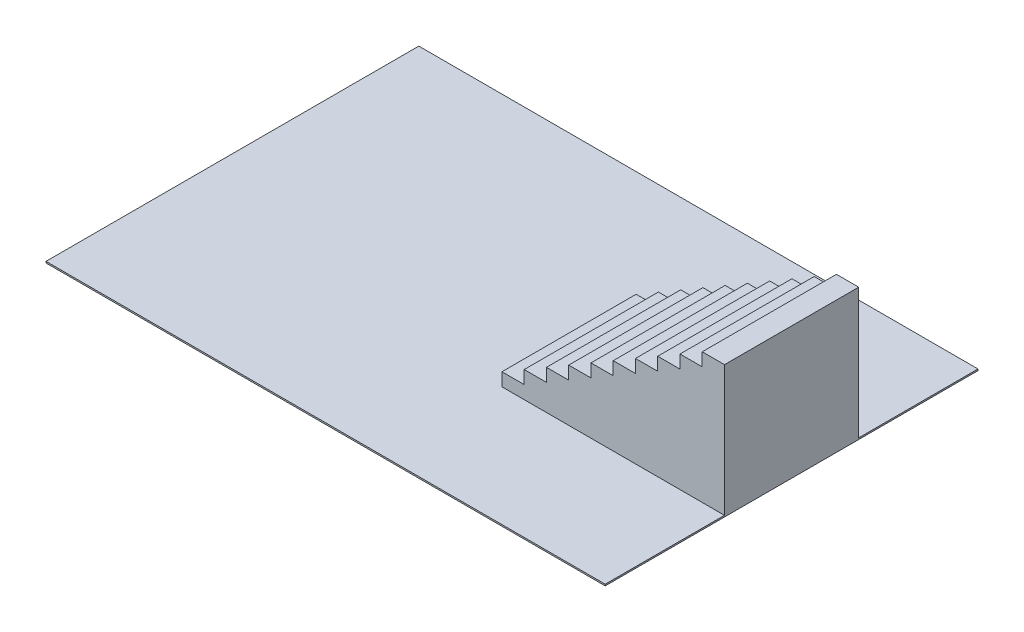
SolidWorks part; units mm, degrees
ref_plane "Front Plane" through (0, 0, 0) normal (0, 0, 1) x (1, 0, 0)
ref_plane "Top Plane" through (0, 0, 0) normal (0, 1, 0) x (1, 0, 0)
ref_plane "Right Plane" through (0, 0, 0) normal (1, 0, 0) x (0, 0, -1)
sketch "Sketch1" plane through (0, 0, 0) normal (0, 1, 0) x (1, 0, 0)
  line L1 (952.5, 635) -> (-952.5, 635)
  line L2 (952.5, 635) -> (952.5, -635)
  line L3 (952.5, -635) -> (-952.5, -635)
  line L4 (-952.5, 635) -> (-952.5, -635)
  line L5 (952.5, 635) -> (-952.5, -635) construction
  line L6 (952.5, -635) -> (-952.5, 635) construction
  point P0 (0, 0)
  dimension "D1" = 1270
  dimension "D2" = 1905
extrude "Boss-Extrude1" add sketch "Sketch1" along normal blind 5.08
sketch "Sketch2" plane through (0, 0, 0) normal (0, 0, 1) x (1, 0, 0)
  line L0 (194.31, 5.08) -> (194.31, 49.53)
  line L1 (-952.5, 5.08) -> (952.5, 5.08) construction
  line L2 (194.31, 49.53) -> (270.129, 49.53)
  line L3 (270.129, 49.53) -> (270.129, 93.98)
  line L4 (270.129, 93.98) -> (345.948, 93.98)
  line L5 (345.948, 93.98) -> (345.948, 138.43)
  line L6 (345.948, 138.43) -> (421.767, 138.43)
  line L7 (421.767, 138.43) -> (421.767, 182.88)
  line L8 (421.767, 182.88) -> (497.586, 182.88)
  line L9 (497.586, 182.88) -> (497.586, 227.33)
  line L10 (497.586, 227.33) -> (573.405, 227.33)
  line L11 (573.405, 227.33) -> (573.405, 271.78)
  line L12 (573.405, 271.78) -> (649.224, 271.78)
  line L13 (649.224, 271.78) -> (649.224, 316.23)
  line L14 (649.224, 316.23) -> (725.043, 316.23)
  line L15 (725.043, 316.23) -> (725.043, 360.68)
  line L16 (725.043, 360.68) -> (800.862, 360.68)
  line L17 (800.862, 360.68) -> (800.862, 405.13)
  line L18 (800.862, 405.13) -> (876.681, 405.13)
  line L19 (876.681, 405.13) -> (876.681, 449.58)
  line L20 (876.681, 449.58) -> (952.5, 449.58)
  line L21 (952.5, 449.58) -> (952.5, 5.08)
  line L22 (194.31, 5.08) -> (952.5, 5.08)
  line L23 (952.5, 5.08) -> (952.5, 0) construction
  point P6 (287.5235, 182.88)
  point P25 (0, 0)
  dimension "D1" = 44.45
  dimension "D2" = 75.819
extrude "Boss-Extrude2" add sketch "Sketch2" along normal mid plane 457.2
